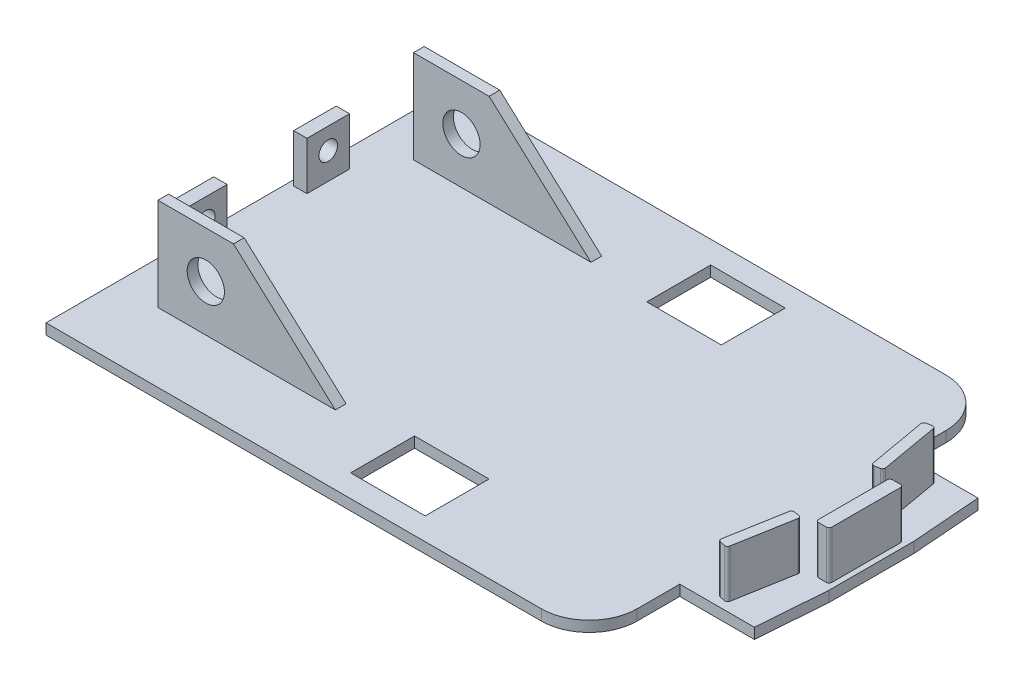
SolidWorks part; units mm, degrees
ref_plane "Plano frontal" through (0, 0, 0) normal (0, 0, 1) x (1, 0, 0)
ref_plane "Plano superior" through (0, 0, 0) normal (0, 1, 0) x (1, 0, 0)
ref_plane "Plano direito" through (0, 0, 0) normal (1, 0, 0) x (0, 0, -1)
sketch "Esboço1" plane through (0, 0, 0) normal (0, 1, 0) x (1, 0, 0)
  line L0 (116, -21) -> (117, -8)
  line L1 (0, 38) -> (102, 38) construction
  line L2 (0, 38) -> (0, -38) construction
  line L3 (0, -38) -> (102, -38) construction
  line L4 (102, 38) -> (102, -38) construction
  line L5 (102, 21) -> (116, 21) construction
  line L6 (102, 21) -> (102, -21) construction
  line L7 (102, -21) -> (116, -21) construction
  line L8 (116, 21) -> (116, -21) construction
  line L9 (117, -8) -> (117, 8)
  line L10 (117, 8) -> (116, 21)
  line L11 (53, -27.8) -> (0, -27.8) construction
  line L12 (53, -33.8) -> (67, -33.8)
  line L13 (53, -33.8) -> (53, -21.8)
  line L14 (53, -21.8) -> (67, -21.8)
  line L15 (67, -33.8) -> (67, -21.8)
  line L16 (53, -27.8) -> (67, -27.8) construction
  line L17 (60, -21.8) -> (60, -33.8) construction
  line L18 (60, -33.8) -> (60, -38) construction
  line L19 (0, 27.8) -> (53, 27.8) construction
  line L20 (53, 27.8) -> (67, 27.8) construction
  line L21 (60, 21.8) -> (60, 33.8) construction
  line L22 (53, 33.8) -> (67, 33.8)
  line L23 (53, 33.8) -> (53, 21.8)
  line L24 (53, 21.8) -> (67, 21.8)
  line L25 (67, 33.8) -> (67, 21.8)
  line L26 (60, 33.8) -> (60, 38) construction
  line L27 (116, 21) -> (102, 21)
  line L28 (116, -21) -> (102, -21)
  line L29 (102, 29) -> (102, 21)
  line L30 (93, 38) -> (0, 38)
  line L31 (0, 38) -> (0, -38)
  line L32 (0, -38) -> (93, -38)
  line L33 (102, -29) -> (102, -21)
  circle A0 centre (93, -29) radius 9 construction
  circle A1 centre (93, 29) radius 9 construction
  arc A2 (93, 38) -> (102, 29) centre (93, 29) cw
  arc A3 (93, -38) -> (102, -29) centre (93, -29) ccw
  point P4 (0, 0)
  point P10 (102, 0)
  point P11 (116, 0)
  point P12 (117, 0)
  point P36 (53, 27.8)
  point P37 (67, 27.8)
  dimension "D7" = 18
  dimension "D1" = 102
  dimension "D2" = 76
  dimension "D3" = 14
  dimension "D4" = 42
  dimension "D5" = 1
  dimension "D6" = 16
  dimension "D8" = 53
  dimension "D9" = 67
  dimension "D10" = 12
  dimension "D11" = 16.2
extrude "Ressalto-extrusão1" add sketch "Esboço1" along normal blind 2
sketch "Esboço2" plane through (0, 2, 0) normal (0, 1, 0) x (1, 0, 0)
  line L0 (111.5, 7.7473) -> (109.5304, 7.4)
  line L1 (113.5, -6.95) -> (116, -6.95)
  line L2 (113.5, -6.95) -> (113.5, 6.95)
  line L3 (113.5, 6.95) -> (116, 6.95)
  line L4 (116, -6.95) -> (116, 6.95)
  line L5 (113.5, -6.95) -> (116, 6.95) construction
  line L6 (113.5, 6.95) -> (116, -6.95) construction
  line L7 (111.5, 7.7473) -> (109.4162, 19.565)
  line L8 (109.5304, 7.4) -> (107.4466, 19.2177)
  line L9 (109.4162, 19.565) -> (107.4466, 19.2177)
  line L10 (111.5, 7.7473) -> (107.4466, 19.2177) construction
  line L11 (109.5304, 7.4) -> (109.4162, 19.565) construction
  line L12 (107.4466, -19.2177) -> (109.5304, -7.4)
  line L13 (107.4466, -19.2177) -> (109.4162, -19.565)
  line L14 (109.5304, -7.4) -> (111.5, -7.7473)
  line L15 (109.4162, -19.565) -> (111.5, -7.7473)
  line L16 (107.4466, -19.2177) -> (111.5, -7.7473) construction
  line L17 (109.5304, -7.4) -> (109.4162, -19.565) construction
  line L18 (109.5304, 7.4) -> (109.5304, -7.4) construction
  line L19 (107.4466, -19.2177) -> (107.4466, 19.2177) construction
  line L20 (111.5, -7.7473) -> (111.5, 7.7473) construction
  line L21 (117, -8) -> (117, 8) construction
  point P0 (114.75, 0)
  point P6 (109.4733, 13.4825)
  point P7 (109.4733, -13.4825)
  point P21 (109.5304, 0)
  dimension "D1" = 2.5
  dimension "D2" = 13.9
  dimension "D3" = 14.8
  dimension "D4" = 2
  dimension "D5" = 2
  dimension "D6" = 170
  dimension "D7" = 2
  dimension "D8" = 1
  dimension "D9" = 12
extrude "Ressalto-extrusão2" add sketch "Esboço2" along normal blind 9
sketch "Esboço3" plane through (0, 2, 0) normal (0, 1, 0) x (1, 0, 0)
  line L0 (2.25, 11.5) -> (2.25, -11.5) construction
  line L1 (0, 38) -> (0, -38) construction
  line L2 (1, -15.5) -> (3.5, -15.5)
  line L3 (1, -15.5) -> (1, -7.5)
  line L4 (1, -7.5) -> (3.5, -7.5)
  line L5 (3.5, -15.5) -> (3.5, -7.5)
  line L6 (1, -15.5) -> (3.5, -7.5) construction
  line L7 (1, -7.5) -> (3.5, -15.5) construction
  line L8 (1, 7.5) -> (3.5, 7.5)
  line L9 (1, 7.5) -> (1, 15.5)
  line L10 (1, 15.5) -> (3.5, 15.5)
  line L11 (3.5, 7.5) -> (3.5, 15.5)
  line L12 (1, 7.5) -> (3.5, 15.5) construction
  line L13 (1, 15.5) -> (3.5, 7.5) construction
  point P2 (2.25, 0)
  dimension "D1" = 2.5
  dimension "D2" = 1
  dimension "D3" = 8
  dimension "D4" = 15
extrude "Ressalto-extrusão3" add sketch "Esboço3" along normal blind 9
sketch "Esboço4" plane through (0, 0, 38) normal (0, 0, 1) x (1, 0, 0)
  line L0 (8.0098, 2) -> (8.0098, 19.4345)
  line L1 (0, 2) -> (93, 2) construction
  line L2 (8.0098, 19.4345) -> (22.2056, 19.4345)
  line L3 (22.2056, 19.4345) -> (41.3305, 2)
  line L4 (41.3305, 2) -> (8.0098, 2)
  circle A0 centre (17.0098, 10.7173) radius 3.5
  point P8 (8.0098, 10.7173)
  dimension "D1" = 7
  dimension "D2" = 9
extrude "Ressalto-extrusão4" add sketch "Esboço4" along normal blind 2 from offset 15 offset against normal yes
mirror "Espelhar1" about plane through (0, 0, 0) normal (0, 0, 1) of "Ressalto-extrusão4"
sketch "Esboço6" plane through (1, 0, 0) normal (-1, 0, 0) x (0, 0, 1)
  line L0 (7.5, 11) -> (15.5, 11) construction
  circle A0 centre (11.5, 7) radius 1.75
  point P4 (11.5, 11)
  dimension "D1" = 4
  dimension "D2" = 3.5
extrude "Corte-extrusão1" cut sketch "Esboço6" against normal up to next (2.5 mm away)
mirror "Espelhar2" about plane through (0, 0, 0) normal (0, 0, 1) of "Corte-extrusão1"
fillet "Filete1" radius 0.5 12 edges at (107.4466, 6.5, -19.2177) (109.4162, 6.5, -19.565) (109.5304, 6.5, -7.4) (111.5, 6.5, -7.7473) (116, 6.5, -6.95) (113.5, 6.5, -6.95) (113.5, 6.5, 6.95) (116, 6.5, 6.95) (111.5, 6.5, 7.7473) (109.5304, 6.5, 7.4) (107.4466, 6.5, 19.2177) (109.4162, 6.5, 19.565)
